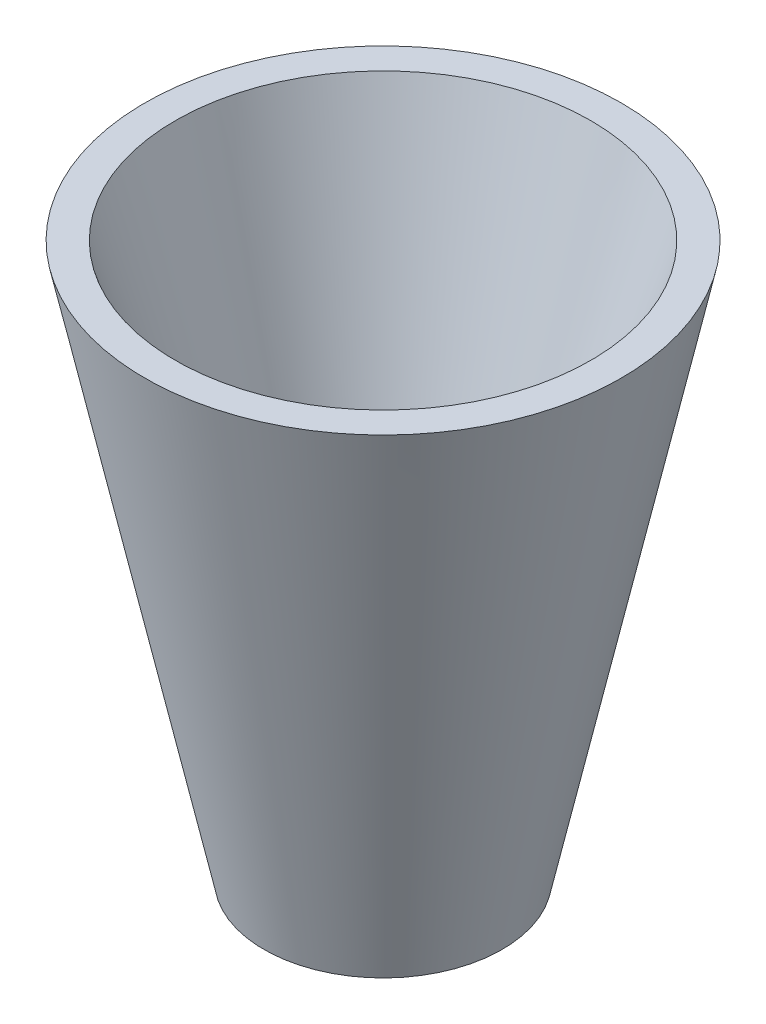
SolidWorks part; units mm, degrees
ref_plane "Front Plane" through (0, 0, 0) normal (0, 0, 1) x (1, 0, 0)
ref_plane "Top Plane" through (0, 0, 0) normal (0, 1, 0) x (1, 0, 0)
ref_plane "Right Plane" through (0, 0, 0) normal (1, 0, 0) x (0, 0, -1)
sketch "Sketch3" plane through (0, 0, 0) normal (0, 0, 1) x (1, 0, 0)
  line L0 (0, 0) -> (12.7, 0)
  line L1 (12.7, 0) -> (25.4, 59.1004)
  line L2 (25.4, 59.1004) -> (22.1403, 59.1004)
  line L3 (22.1403, 59.1004) -> (9.2281, 16.9829)
  line L5 (0, 10.16) -> (0, 0)
  line L6 (0, 0) -> (0, 64.1456) construction
  line L7 (-33.9711, 10.16) -> (34.5135, 10.16) construction
  arc A0 (9.2281, 16.9829) -> (0, 10.16) centre (0, 19.812) cw
  point P9 (31.8336, 9.8733)
  point P10 (0, 0)
  point P11 (0, 0)
  point P12 (0, 0)
  point P13 (0, 0)
  dimension "D4" = 9.652
  dimension "D1" = 25.4
  dimension "D2" = 12.7
  dimension "D3" = 10.16
  dimension "D5" = 3.2597
  dimension "D6" = 10.16
revolve "Revolve1" add sketch "Sketch3" angle 360 about L6
